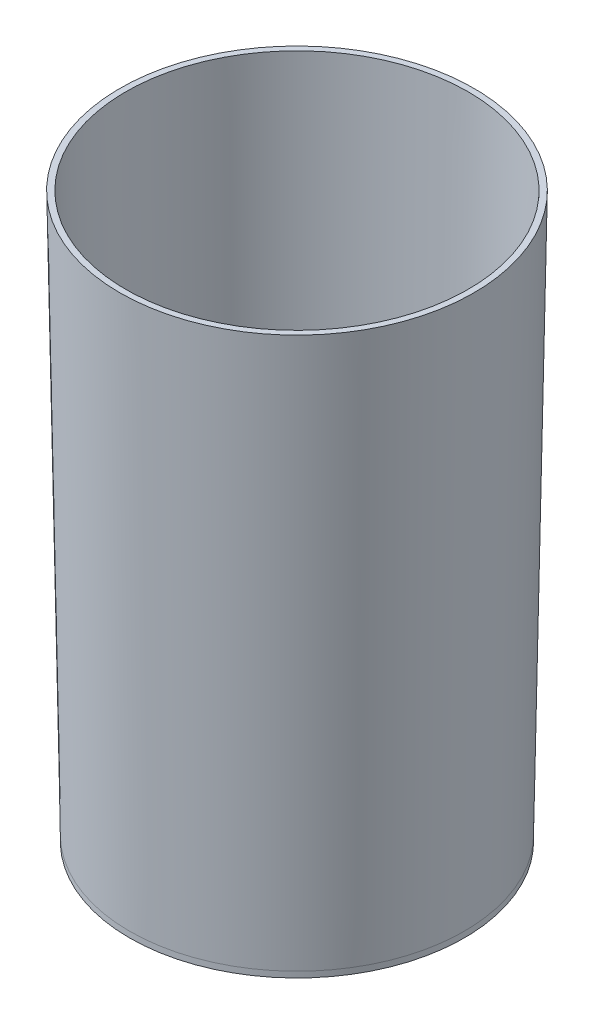
SolidWorks part; units mm, degrees
ref_plane "Front Plane" through (0, 0, 0) normal (0, 0, 1) x (1, 0, 0)
ref_plane "Top Plane" through (0, 0, 0) normal (0, 1, 0) x (1, 0, 0)
ref_plane "Right Plane" through (0, 0, 0) normal (1, 0, 0) x (0, 0, -1)
sketch "Sketch1" plane through (0, 0, 0) normal (0, 1, 0) x (1, 0, 0)
  circle A0 centre (0, 0) radius 57.15
  dimension "D1" = 114.3
extrude "Boss-Extrude1" add sketch "Sketch1" along normal blind 190.5 draft 1 draft outward yes
sketch "Sketch3" plane through (0, 0, 0) normal (0, -1, 0) x (1, 0, 0)
  circle A0 centre (0, 0) radius 55.15
  circle A1 centre (0, 0) radius 57.15
  circle A2 centre (0, 0) radius 57.15
  dimension "D2" = 2
  dimension "D1" = 0
extrude "Cut-Extrude1" cut sketch "Sketch3" against normal blind 190.5 draft 1 contours A0 draft outward yes
sketch "Sketch4" plane through (0, 0, 0) normal (0, -1, 0) x (1, 0, 0)
  circle A1 centre (0, 0) radius 57.15
  circle A2 centre (0, 0) radius 57.15
  dimension "D1" = 0
extrude "Boss-Extrude2" add sketch "Sketch4" along normal blind 2
